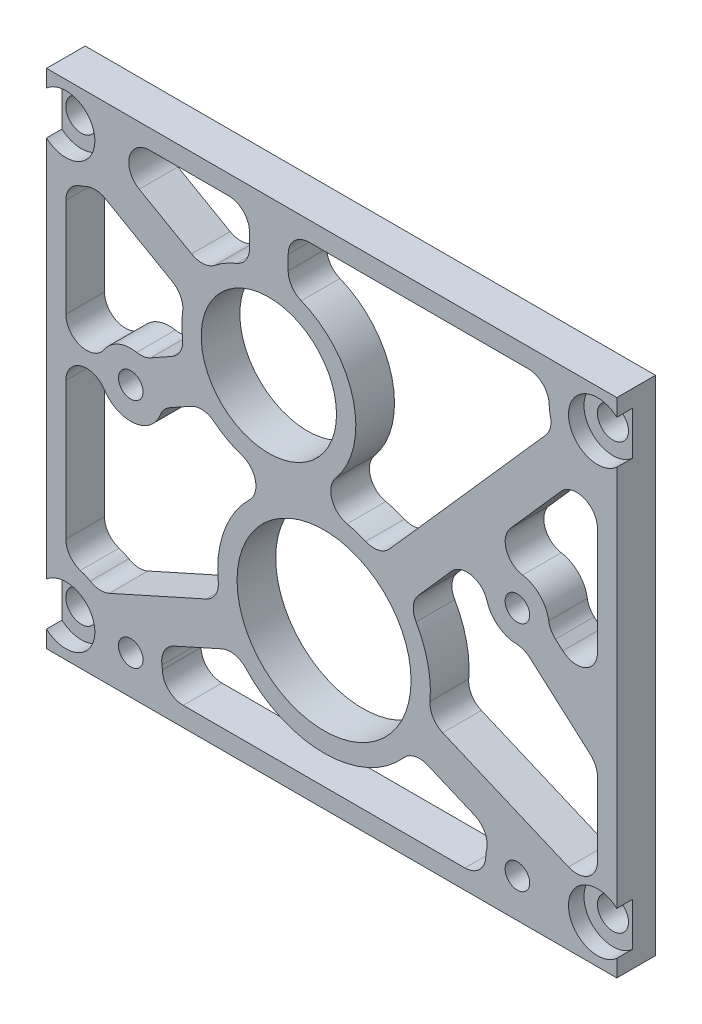
SolidWorks part; units mm, degrees
material "6061-T6 (SS)"
ref_plane "Front Plane" through (0, 0, 0) normal (0, 0, 1) x (1, 0, 0)
ref_plane "Top Plane" through (0, 0, 0) normal (0, 1, 0) x (1, 0, 0)
ref_plane "Right Plane" through (0, 0, 0) normal (1, 0, 0) x (0, 0, -1)
sketch "Sketch1" plane through (0, 0, 0) normal (0, 0, 1) x (1, 0, 0)
  line L0 (13.2944, 76.327) -> (33.6481, 76.327) construction
  line L1 (50.8, -983.6249) -> (50.8, 49016.3751) construction
  line L2 (-30.1625, -1019.5657) -> (-30.1625, 48980.4343) construction
  line L11 (-36.5125, 25.4) -> (57.15, 25.4)
  line L12 (-36.5125, 25.4) -> (-36.5125, -57.15)
  line L13 (-36.5125, -57.15) -> (57.15, -57.15)
  line L14 (57.15, 25.4) -> (57.15, -57.15)
  circle A0 centre (0, 0) radius 11.1125
  circle A2 centre (0, 0) radius 11.43 construction
  circle A3 centre (9.0696, -31.75) radius 21.59 construction
  circle A4 centre (9.0696, -31.75) radius 14.2875
  dimension "D1" = 22.225
  dimension "D4" = 6.35
  dimension "D5" = 43.18
  dimension "D6" = 28.575
  dimension "D8" = 22.86
  dimension "D10" = 82.55
  dimension "D2" = 57.15
  dimension "D3" = 50.8
  dimension "D7" = 30.1625
  dimension "D9" = 25.4
  dimension "D11" = 6.35
extrude "Boss-Extrude1" add sketch "Sketch1" along normal blind 6.35
hole_wizard "CBORE for #10 Binding Head Machine Screw1" positions "Sketch2" profile "Sketch3" counterbore size "#10" standard "ANSI Inch" end condition through all
sketch "Sketch2" plane through (0, 0, 6.35) normal (0, 0, 1) x (1, 0, 0)
  point P0 (-33.3375, 19.05)
  point P3 (53.975, 19.05)
  point P7 (-33.3375, -50.8)
  point P10 (53.975, -50.8)
sketch "Sketch3" plane through (-33.3375, 19.05, 6.35) normal (1, 0, 0) x (0, -1, 0)
  line L0 (0, 0) -> (0, 6.35)
  line L1 (0, 6.35) -> (2.5527, 6.35)
  line L2 (2.5527, 6.35) -> (2.5527, 2.54)
  line L3 (2.5527, 2.54) -> (4.7625, 2.54)
  line L4 (4.7625, 2.54) -> (4.7625, 0)
  line L5 (4.7625, 0) -> (0, 0)
  line L6 (0, -6.35) -> (0, 107.95) construction
  dimension "Thru Hole Dia." = 5.1054
  dimension "Thru Hole Depth" = 6.35
  dimension "C'Bore Dia." = 9.525
  dimension "C'Bore Depth" = 2.54
hole_wizard "#10-32 Tapped Hole1" positions "Sketch5" profile "Sketch6" tap size "#10-32" standard "ANSI Inch" end condition through all
sketch "Sketch5" plane through (0, 0, 6.35) normal (0, 0, 1) x (1, 0, 0)
  line L0 (-36.5125, -57.15) -> (57.15, -57.15) construction
  circle A0 centre (9.0696, -31.75) radius 14.2875 construction
  point P0 (-22.6804, -12.7)
  point P2 (-22.6804, -50.8)
  point P4 (40.8196, -12.7)
  point P6 (40.8196, -50.8)
  dimension "D4" = 31.75
  dimension "D1" = 38.1
  dimension "D2" = 6.35
  dimension "D3" = 31.75
sketch "Sketch6" plane through (-22.6804, -12.7, 6.35) normal (1, 0, 0) x (0, -1, 0)
  line L0 (0, 0) -> (0, 6.35)
  line L1 (0, 6.35) -> (2.0193, 6.35)
  line L2 (2.0193, 6.35) -> (2.0193, 0)
  line L5 (2.0193, 0) -> (0, 0)
  line L11 (0, -6.35) -> (0, 107.95) construction
  dimension "Thru Tap Drill Dia." = 4.0386
  dimension "Thru Tap Drill Depth" = 6.35
cosmetic thread "Hole Thread1" parameters "D2"=4.826
cosmetic thread "Hole Thread2" parameters "D2"=4.826
cosmetic thread "Hole Thread3" parameters "D2"=4.826
cosmetic thread "Hole Thread4" parameters "D2"=4.826
sketch "Sketch4" plane through (0, 0, 0) normal (0, 0, 1) x (1, 0, 0)
  line L0 (9.0696, -31.75) -> (53.975, -50.8) construction
  line L1 (48.0475, 12.3445) -> (9.0696, -31.75) construction
  line L2 (-36.5125, -53.975) -> (57.15, -53.975)
  line L3 (-18.5694, -53.975) -> (36.7086, -53.975)
  line L4 (-25.435, -47.2501) -> (9.0696, -31.75) construction
  line L5 (-33.3375, 15.5002) -> (-33.3375, -47.2502)
  line L6 (-33.3375, 11.1125) -> (-33.3375, -7.9973)
  line L7 (0, 0) -> (-33.3375, 19.05) construction
  line L8 (57.15, 22.225) -> (-36.5125, 22.225)
  line L9 (46.7002, 22.225) -> (3.175, 22.225)
  line L10 (0, 0) -> (0, 22.225) construction
  line L11 (53.975, -47.2502) -> (53.975, 15.5002)
  line L12 (53.975, -42.1717) -> (53.975, -28.5665)
  line L13 (-3.175, 13.9303) -> (-3.175, 22.225)
  line L14 (-10.5196, 9.668) -> (-21.2835, 15.8188)
  line L15 (46.778, 15.7022) -> (18.0634, -16.7817)
  line L16 (10.3096, -28.8271) -> (53.6015, -47.1927) construction
  line L17 (-18.5571, -47.641) -> (-5.293, -41.6826)
  line L18 (3.175, 13.9303) -> (3.175, 22.225)
  line L19 (-13.6701, 4.1547) -> (-28.5964, 12.684)
  line L20 (47.9769, 7.4706) -> (39.6726, -1.9237)
  line L21 (26.1174, -35.5332) -> (49.2069, -45.3283)
  line L22 (-28.0025, -44.9228) -> (-7.895, -35.8902)
  line L23 (3.175, -5.4711) -> (-34.9127, 16.2933) construction
  line L24 (-3.175, 5.4711) -> (-31.7623, 21.8067) construction
  line L25 (-3.175, 22.225) -> (-19.5822, 22.225)
  line L26 (3.175, -5.4711) -> (3.175, 22.225) construction
  line L27 (-3.175, 5.4711) -> (-3.175, 22.225) construction
  line L28 (51.5962, 21.1528) -> (6.6908, -29.6472) construction
  line L29 (53.975, 19.05) -> (9.0696, -31.75) construction
  line L30 (56.3538, 16.9472) -> (11.4484, -33.8528) construction
  line L31 (-33.3375, -50.8) -> (9.0696, -31.75) construction
  line L32 (9.0696, -31.75) -> (52.3615, -50.1155) construction
  line L33 (-34.6385, -47.9038) -> (7.7686, -28.8538) construction
  line L34 (53.975, -20.0913) -> (53.975, 5.1996)
  line L35 (-32.0365, -53.6962) -> (10.3706, -34.6462) construction
  line L36 (23.6375, -41.3789) -> (37.1588, -47.115)
  line L37 (-33.3375, -17.4027) -> (-33.3375, -42.8625)
  line L38 (-22.6804, -12.7) -> (0, 0) construction
  line L39 (-17.5422, -13.4617) -> (-10.6032, -9.5762)
  line L40 (-20.6447, -7.9212) -> (-13.7057, -4.0357)
  line L41 (29.9841, -12.8841) -> (22.8211, -20.9873)
  line L42 (-25.0367, -10.3806) -> (-1.5512, 2.7703) construction
  line L43 (-21.9343, -15.9211) -> (1.5512, -2.7703) construction
  line L44 (40.8196, -12.7) -> (32.4495, -5.3011) construction
  line L49 (-23.4855, -13.1508) -> (0, 0) construction
  line L50 (40.8196, -12.7) -> (53.975, -24.3289) construction
  line L51 (46.0025, -13.0439) -> (53.975, -20.0913)
  line L52 (41.7969, -17.8015) -> (53.975, -28.5665)
  arc A0 (-27.0343, -15.5327) -> (-17.5422, -13.4617) centre (-22.6804, -12.7) ccw
  circle A1 centre (9.0696, -31.75) radius 14.2875 construction
  arc A2 (-33.3375, -7.9973) -> (-27.0343, -9.8673) centre (-29.9085, -7.9973) ccw
  arc A3 (-13.6701, 4.1547) -> (-13.7057, -4.0357) centre (0, 0) ccw
  arc A4 (-3.175, 13.9303) -> (-10.5196, 9.668) centre (0, 0) ccw
  arc A5 (-19.5822, 22.225) -> (-21.2835, 15.8188) centre (-19.5822, 18.796) ccw
  circle A6 centre (9.0696, -31.75) radius 17.4625
  arc A7 (35.8403, -14.1788) -> (41.7969, -17.8015) centre (40.8196, -12.7) ccw
  arc A8 (-28.0025, -44.9228) -> (-33.3375, -42.8625) centre (-33.3375, -50.8) ccw
  arc A9 (-3.1495, -19.2748) -> (-7.895, -35.8902) centre (9.0696, -31.75) ccw
  circle A10 centre (-22.6804, -12.7) radius 2.0193 construction
  arc A11 (49.2069, -45.3283) -> (53.975, -42.1717) centre (50.546, -42.1717) ccw
  arc A12 (-38.6292, 13.1337) -> (-38.6292, 24.9663) centre (-33.3375, 19.05) ccw
  arc A13 (-33.3375, 11.1125) -> (-28.5964, 12.684) centre (-33.3375, 19.05) ccw
  arc A14 (53.975, 5.1996) -> (47.9769, 7.4706) centre (50.546, 5.1996) ccw
  arc A15 (39.6726, -1.9237) -> (41.6762, -7.5768) centre (42.2417, -4.1948) ccw
  arc A16 (46.0025, -13.0439) -> (41.6762, -7.5768) centre (40.8196, -12.7) ccw
  arc A17 (59.2667, 24.9663) -> (59.2667, 13.1337) centre (53.975, 19.05) ccw
  arc A18 (46.7002, 22.225) -> (46.778, 15.7022) centre (53.975, 19.05) ccw
  arc A19 (-36.5125, -54.3498) -> (-36.5125, -47.2502) centre (-33.3375, -50.8) ccw construction
  arc A20 (-36.5125, -54.3498) -> (-36.5125, -47.2502) centre (-33.3375, -50.8) ccw construction
  arc A21 (-20.6447, -7.9212) -> (-27.0343, -9.8673) centre (-22.6804, -12.7) ccw
  arc A22 (37.1588, -47.115) -> (36.7086, -53.975) centre (40.8196, -50.8) ccw
  circle A23 centre (40.8196, -50.8) radius 2.0193 construction
  arc A24 (-27.0343, -15.5327) -> (-33.3375, -17.4027) centre (-29.9085, -17.4027) ccw
  circle A25 centre (40.8196, -12.7) radius 2.0193 construction
  arc A26 (-10.6032, -9.5762) -> (-4.4749, -13.5686) centre (0, 0) ccw
  arc A27 (10.9668, -9.1576) -> (12.8555, -14.7028) centre (13.5989, -11.3554) ccw
  arc A29 (35.8403, -14.1788) -> (29.9841, -12.8841) centre (32.5532, -15.1551) ccw
  arc A30 (-3.1495, -19.2748) -> (-4.4749, -13.5686) centre (-5.5489, -16.8251) ccw
  arc A31 (18.0634, -16.7817) -> (12.8555, -14.7028) centre (9.0696, -31.75) ccw
  circle A32 centre (0, 0) radius 14.2875
  arc A33 (10.9668, -9.1576) -> (3.175, 13.9303) centre (0, 0) ccw
  arc A34 (-5.293, -41.6826) -> (23.6375, -41.3789) centre (9.0696, -31.75) ccw
  arc A35 (26.1174, -35.5332) -> (22.8211, -20.9873) centre (9.0696, -31.75) ccw
  circle A36 centre (-22.6804, -50.8) radius 5.1943
  arc A37 (-18.5694, -53.975) -> (-18.5571, -47.641) centre (-22.6804, -50.8) ccw
  dimension "D2" = 3.429
  dimension "D5" = 3.175
  dimension "D7" = 3.175
  dimension "D15" = 3.175
  dimension "D16" = 3.175
  dimension "D17" = 3.429
  dimension "D23" = 3.175
  dimension "D8" = 3.175
  dimension "D18" = 3.175
  dimension "D22" = 3.175
  dimension "D1" = 3.175
  dimension "D3" = 3.175
  dimension "D4" = 3.175
  dimension "D6" = 3.175
  dimension "D9" = 3.175
  dimension "D10" = 3.175
  dimension "D11" = 3.175
  dimension "D12" = 3.175
  dimension "D13" = 3.175
  dimension "D14" = 3.175
  dimension "D19" = 3.175
  dimension "D24" = 3.175
extrude "Cut-Extrude1" cut sketch "Sketch4" along normal through all
fillet "Fillet1" radius 3.429 30 edges at (46.778, 15.7022, 3.175) (46.7002, 22.225, 3.175) (3.175, 13.9303, 3.175) (3.175, 22.225, 3.175) (-3.175, 22.225, 3.175) (-3.175, 13.9303, 3.175) (-10.5196, 9.668, 3.175) (-33.3375, 11.1125, 3.175) (-28.5964, 12.684, 3.175) (-13.6701, 4.1547, 3.175) (-28.0025, -44.9228, 3.175) (-33.3375, -42.8625, 3.175) (-10.6032, -9.5762, 3.175) (-13.7057, -4.0357, 3.175) (-5.293, -41.6826, 3.175) (23.6375, -41.3789, 3.175) (26.1174, -35.5332, 3.175) (22.8211, -20.9873, 3.175) (18.0634, -16.7817, 3.175) (-7.895, -35.8902, 3.175) (-17.5422, -13.4617, 3.175) (-18.5694, -53.975, 3.175) (-18.5571, -47.641, 3.175) (36.7086, -53.975, 3.175) (37.1588, -47.115, 3.175) (53.975, -28.5665, 3.175) (41.7969, -17.8015, 3.175) (46.0025, -13.0439, 3.175) (53.975, -20.0913, 3.175) (-20.6447, -7.9212, 3.175)
hole_wizard "#4-40 Tapped Hole1" positions "Sketch7" profile "Sketch8" tap size "#4-40" standard "ANSI Inch"
sketch "Sketch7" plane through (0, 25.4, 6.35) normal (0, 1, 0) x (1, 0, 0)
  point P0 (48.4188, 87.3125)
  point P6 (-27.7812, 87.3125)
  point P9 (-27.7812, 3.175)
  point P15 (48.4188, 3.175)
sketch "Sketch8" plane through (48.4188, 25.4, -80.9625) normal (1, 0, 0) x (0, 0, 1)
  line L0 (0, 0) -> (0, 10.8392)
  line L1 (0, 10.8392) -> (1.1303, 10.16)
  line L2 (1.1303, 10.16) -> (1.1303, 0)
  line L3 (1.1303, 0) -> (0, 0)
  line L4 (0, 10.8392) -> (-1.1303, 10.16) construction
  line L5 (0, -6.35) -> (0, 107.95) construction
  dimension "Tap Drill Dia." = 2.2606
  dimension "Tap Drill Depth" = 10.16
  dimension "Drill Angle" = 118
cosmetic thread "Hole Thread5" [suppressed] parameters "D1"=8.128, "D2"=2.8448
cosmetic thread "Hole Thread7" [suppressed] parameters "D1"=8.128, "D2"=2.8448
